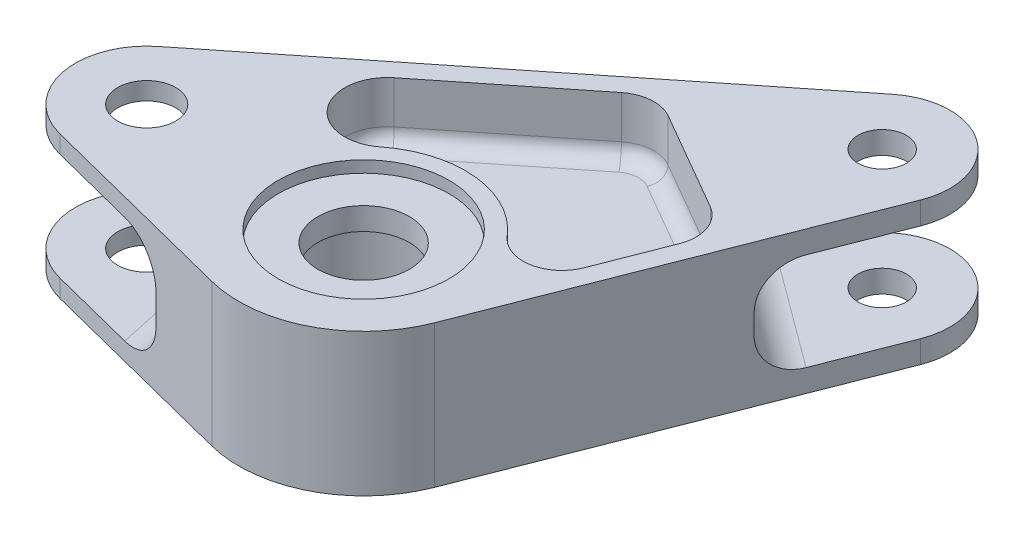
SolidWorks part; units mm, degrees
material "6061 Alloy"
ref_plane "Front Plane" through (0, 0, 0) normal (0, 0, 1) x (1, 0, 0)
ref_plane "Top Plane" through (0, 0, 0) normal (0, 1, 0) x (1, 0, 0)
ref_plane "Right Plane" through (0, 0, 0) normal (1, 0, 0) x (0, 0, -1)
sketch "Layout" plane through (0, 0, 0) normal (0, 1, 0) x (1, 0, 0)
  line L0 (0, 0) -> (-35.56, 0) construction
  line L1 (0, 0) -> (31.115, 53.8928) construction
  dimension "D1" = 35.56
  dimension "D2" = 62.23
  dimension "D3" = 120
sketch "Sketch2" plane through (0, 0, 0) normal (0, 1, 0) x (1, 0, 0)
  line L0 (-42.844, 9.1356) -> (24.1872, 62.5815)
  line L1 (-38.4393, -11.3237) -> (-5.0387, -19.8164)
  line L2 (19.0408, -7.4517) -> (41.4633, 49.8429)
  arc A0 (-5.0387, -19.8164) -> (19.0408, -7.4517) centre (0, 0) ccw
  arc A1 (-42.844, 9.1356) -> (-38.4393, -11.3237) centre (-35.56, 0) ccw
  arc A2 (41.4633, 49.8429) -> (24.1872, 62.5815) centre (31.115, 53.8928) ccw
  dimension "D1" = 20.447
  dimension "D2" = 11.684
  dimension "D3" = 11.1125
extrude "Boss-Extrude2" add sketch "Sketch2" along normal mid plane 23.368
sketch "Sketch3" plane through (0, -11.684, 0) normal (0, -1, 0) x (1, 0, 0)
  circle A0 centre (0, 0) radius 12
  dimension "D1" = 24
extrude "Cut-Extrude1" cut sketch "Sketch3" against normal blind 17.78
sketch "Sketch5" plane through (0, 11.684, 0) normal (0, 1, 0) x (1, 0, 0)
  circle A0 centre (-35.56, 0) radius 4.7625
  circle A1 centre (31.115, 53.8928) radius 3.9688
  dimension "D1" = 9.525
  dimension "D2" = 7.9375
extrude "Cut-Extrude3" cut sketch "Sketch5" against normal through all
sketch "Sketch4" plane through (0, 11.684, 0) normal (0, 1, 0) x (1, 0, 0)
  circle A0 centre (0, 0) radius 7.5
  dimension "D1" = 15
extrude "Cut-Extrude2" cut sketch "Sketch4" against normal through all
sketch "Sketch6" plane through (0, 11.684, 0) normal (0, 1, 0) x (1, 0, 0)
  line L0 (8.8106, 41.107) -> (25.1475, 31.6749)
  line L1 (-19.0511, 24.0457) -> (1.6769, 40.5727)
  line L2 (23.4812, 12.6066) -> (27.8858, 23.8614)
  line L6 (0, 0) -> (31.115, 53.8928) construction
  line L8 (-42.844, 9.1356) -> (24.1872, 62.5815) construction
  line L9 (19.0408, -7.4517) -> (41.4633, 49.8429) construction
  arc A0 (12.728, 10.8101) -> (-10.3583, 13.0983) centre (0, 0) ccw
  arc A2 (23.4812, 12.6066) -> (12.728, 10.8101) centre (17.5679, 14.9208) cw
  arc A3 (27.8858, 23.8614) -> (25.1475, 31.6749) centre (21.9725, 26.1756) ccw
  arc A4 (8.8106, 41.107) -> (1.6769, 40.5727) centre (5.6356, 35.6077) ccw
  circle A5 centre (31.115, 53.8928) radius 19.05 construction
  circle A6 centre (-35.56, 0) radius 19.05 construction
  arc A7 (-10.3583, 13.0983) -> (-19.0511, 24.0457) centre (-14.6937, 18.5807) cw
  dimension "D1" = 27.94
  dimension "D3" = 3.175
  dimension "D4" = 3.175
  dimension "D5" = 22.225
  dimension "D6" = 38.1
  dimension "D7" = 16.6991
  dimension "D8" = 38.1
  dimension "D9" = 6.35
extrude "Cut-Extrude4" cut sketch "Sketch6" against normal blind 9.525
sketch "Sketch8" plane through (0, -11.684, 0) normal (0, -1, 0) x (1, 0, 0)
  line L0 (25.1475, -31.6749) -> (8.8106, -41.107)
  line L1 (0, 0) -> (31.115, -53.8928) construction
  line L2 (-13.416, -28.5387) -> (1.6769, -40.5727)
  line L4 (27.8858, -23.8614) -> (24.4414, -15.0602)
  line L6 (-42.844, -9.1356) -> (24.1872, -62.5815) construction
  line L7 (19.0408, 7.4517) -> (41.4633, -49.8429) construction
  arc A0 (-7.0929, -17.6803) -> (13.8961, -13.0308) centre (0, 0) ccw
  arc A1 (24.4414, -15.0602) -> (13.8961, -13.0308) centre (18.5281, -17.3744) ccw
  arc A2 (25.1475, -31.6749) -> (27.8858, -23.8614) centre (21.9725, -26.1756) ccw
  circle A3 centre (31.115, -53.8928) radius 19.05 construction
  arc A4 (8.8106, -41.107) -> (1.6769, -40.5727) centre (5.6356, -35.6077) cw
  circle A5 centre (-35.56, 0) radius 19.05 construction
  arc A6 (-13.416, -28.5387) -> (-7.0929, -17.6803) centre (-9.4572, -23.5737) cw
  point P22 (-35.9678, 9.525)
  dimension "D1" = 22.225
  dimension "D3" = 3.175
  dimension "D4" = 38.1
  dimension "D5" = 3.175
  dimension "D6" = 19.05
  dimension "D7" = 6.35
extrude "Cut-Extrude5" cut sketch "Sketch8" against normal blind 9.525
sketch "Sketch10" plane through (0, 11.684, 0) normal (0, 1, 0) x (1, 0, 0)
  circle A0 centre (0, 0) radius 14
  dimension "D1" = 28
extrude "Cut-Extrude6" cut sketch "Sketch10" against normal blind 1.905
sketch "Sketch11" plane through (0, 11.684, 0) normal (0, 1, 0) x (1, 0, 0)
  line L0 (7.7168, 49.4492) -> (33.7864, 30.2267) construction
  line L1 (-42.844, 9.1356) -> (24.1872, 62.5815) construction
  line L2 (19.0408, -7.4517) -> (41.4633, 49.8429) construction
  line L3 (-25.8322, 22.6996) -> (-17.3529, -16.6853) construction
  line L4 (-38.4393, -11.3237) -> (-5.0387, -19.8164) construction
  line L5 (-42.844, 9.1356) -> (-25.8322, 22.6996) construction
  line L6 (-38.4393, -11.3237) -> (-17.3529, -16.6853) construction
  line L7 (24.1872, 62.5815) -> (7.7168, 49.4492) construction
  line L8 (41.4633, 49.8429) -> (33.7864, 30.2267) construction
  circle A0 centre (-35.56, 0) radius 14.2875 construction
  circle A1 centre (31.115, 53.8928) radius 17.4625 construction
  dimension "D1" = 28.575
  dimension "D2" = 34.925
ref_plane "Plane1" through (-20.0173, 0, 4.3096) normal (-0.9776, 0, 0.2105) x (0.2105, 0, 0.9776)
ref_plane "Plane2" through (26.3376, 0, -35.719) normal (-0.5935, 0, 0.8049) x (0.8049, 0, 0.5935)
sketch "Sketch12" plane through (26.3376, 0, -35.719) normal (-0.5935, 0, 0.8049) x (0.8049, 0, 0.5935)
  line L0 (-6.9403, 9.3704) -> (-6.9403, -11.0985) construction
  line L1 (12.1097, 8.001) -> (-25.9903, 8.001)
  line L2 (12.1097, 8.001) -> (12.1097, -8.001)
  line L3 (12.1097, -8.001) -> (-25.9903, -8.001)
  line L4 (-23.1354, 11.684) -> (9.2547, 11.684) construction
  line L5 (-23.1354, 11.684) -> (9.2547, 11.684) construction
  line L6 (-17.6727, -11.684) -> (3.792, -11.684) construction
  line L7 (-17.6727, -11.684) -> (3.792, -11.684) construction
  line L8 (-25.9903, 8.001) -> (-25.9903, -8.001)
  line L9 (-24.218, 0) -> (7.7049, 0) construction
  point P5 (12.1097, 0)
  point P6 (-6.9403, -8.001)
  dimension "D1" = 16.002
  dimension "D4" = 38.1
extrude "Cut-Extrude7" cut sketch "Sketch12" against normal up to next
sketch "Sketch15" plane through (-20.0173, 0, 4.3096) normal (-0.9776, 0, 0.2105) x (0.2105, 0, 0.9776)
  line L0 (-7.4844, 9.5144) -> (-7.4844, -9.5144) construction
  line L1 (0, 0) -> (-46.1367, 0) construction
  line L3 (-17.9484, -11.684) -> (2.9796, -11.684) construction
  line L4 (-17.9484, -11.684) -> (2.9796, -11.684) construction
  line L6 (-32.8844, 8.7884) -> (17.9156, 8.7884)
  line L7 (17.9156, 8.7884) -> (17.9156, -8.7884)
  line L8 (17.9156, -8.7884) -> (-32.8844, -8.7884)
  line L9 (-32.8844, -8.7884) -> (-32.8844, 8.7884)
  point P2 (-32.8844, 0)
  point P7 (-7.4844, 0)
  point P13 (-7.4844, 8.7884)
  dimension "D1" = 17.5768
  dimension "D2" = 50.8
extrude "Cut-Extrude8" cut sketch "Sketch15" along normal up to next
fillet "Fillet2" radius 3.175 8 edges at (4.1201, -2.159, -18.5991) (-5.8695, -2.159, -34.5557) (26.1636, -2.159, -19.4608) (-14.9447, -2.159, -20.3783) (19.7281, -2.159, -11.1388) (27.9652, -2.159, -28.2758) (16.9791, -2.159, -36.3909) (5.1614, -2.159, -41.94)
fillet "Fillet3" radius 6.35 4 edges at (20.7516, 8.001, -39.8379) (20.7516, -8.001, -39.8379) (-21.5925, 8.7884, -3.0071) (-21.5925, -8.7884, -3.0071)
fillet "Fillet4" radius 2.54 8 edges at (18.6143, 2.159, -8.6576) (1.6471, 2.159, -16.6177) (-20.1674, 2.159, -14.2343) (-8.6871, 2.159, -32.3092) (5.1614, 2.159, -41.94) (16.9791, 2.159, -36.3909) (27.9652, 2.159, -28.2758) (25.6835, 2.159, -18.234)
sketch "Sketch16" plane through (0, -11.684, 0) normal (0, -1, 0) x (1, 0, 0)
  circle A0 centre (0, 0) radius 17.272
  dimension "D1" = 34.544
extrude "Cut-Extrude9" cut sketch "Sketch16" against normal blind 3.048
